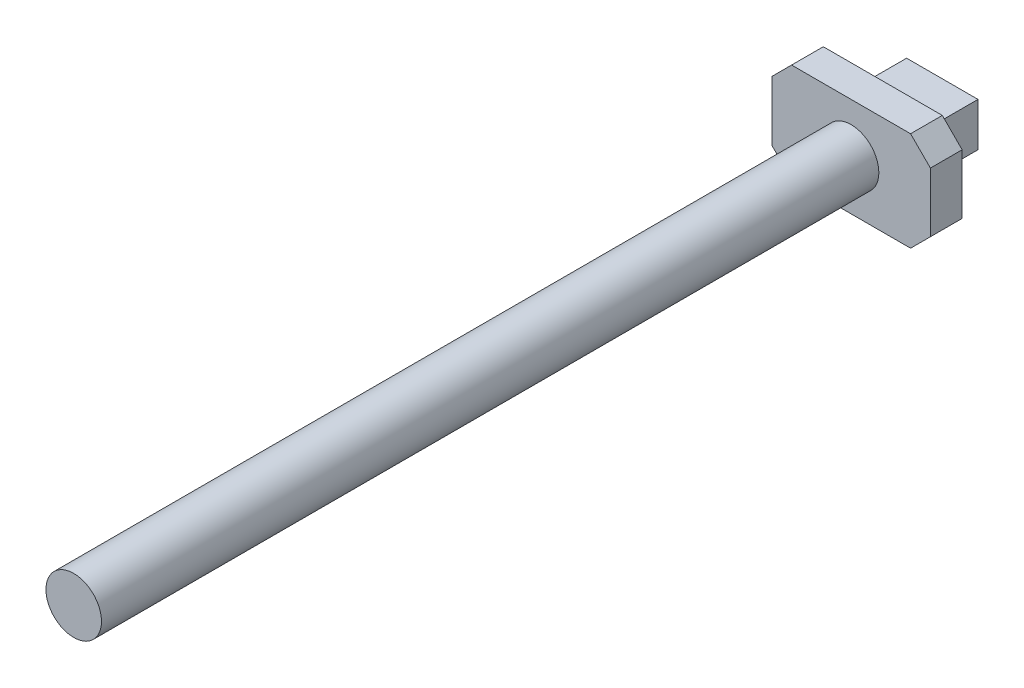
SolidWorks part; units mm, degrees
ref_plane "前视基准面" through (0, 0, 0) normal (0, 0, 1) x (1, 0, 0)
ref_plane "上视基准面" through (0, 0, 0) normal (0, 1, 0) x (1, 0, 0)
ref_plane "右视基准面" through (0, 0, 0) normal (1, 0, 0) x (0, 0, -1)
sketch "草图1" plane through (0, 0, 0) normal (0, 0, 1) x (1, 0, 0)
  circle A0 centre (0, 0) radius 7
extrude "凸台-拉伸1" add sketch "草图1" along normal blind 160 and the other way blind 36
sketch "草图2" plane through (0, 0, -36) normal (0, 0, -1) x (-1, 0, 0)
  line L0 (15, 12.5) -> (20, 7.5)
  line L1 (-20, 12.5) -> (20, 12.5)
  line L2 (-20, 12.5) -> (-20, -12.5)
  line L3 (-20, -12.5) -> (20, -12.5)
  line L4 (20, 12.5) -> (20, -12.5)
  line L5 (-20, 12.5) -> (20, -12.5) construction
  line L6 (-20, -12.5) -> (20, 12.5) construction
  line L7 (-15, 12.5) -> (-20, 7.5)
  line L8 (-20, -7.5) -> (-15, -12.5)
  line L9 (-15, -12.5) -> (15, -12.5)
  line L10 (15, -12.5) -> (20, -7.5)
  point P0 (0, 0)
  circle M1 centre (0, 0) radius 7
  dimension "D1" = 25
  dimension "D2" = 40
  dimension "D3" = 5
  dimension "D4" = 5
  dimension "D5" = 5
  dimension "D6" = 5
  dimension "D7" = 5
  dimension "D8" = 5
  dimension "D9" = 5
  dimension "D10" = 5
extrude "凸台-拉伸2" add sketch "草图2" along normal blind 8 contours L3 L10 L4 L0 L1 L7 L2 L8 M1 | M1
sketch "草图3" plane through (0, 0, -44) normal (0, 0, -1) x (-1, 0, 0)
  line L1 (9, 5.5) -> (-9, 5.5)
  line L2 (9, 5.5) -> (9, -5.5)
  line L3 (9, -5.5) -> (-9, -5.5)
  line L4 (-9, 5.5) -> (-9, -5.5)
  line L5 (9, 5.5) -> (-9, -5.5) construction
  line L6 (9, -5.5) -> (-9, 5.5) construction
  point P0 (0, 0)
  dimension "D1" = 18
  dimension "D2" = 11
extrude "凸台-拉伸3" add sketch "草图3" along normal blind 15
sketch "草图4" plane through (0, 0, -59) normal (0, 0, -1) x (-1, 0, 0)
  line L1 (15, 12.5) -> (-15, 12.5)
  line L2 (15, 12.5) -> (15, -12.5)
  line L3 (15, -12.5) -> (-15, -12.5)
  line L4 (-15, 12.5) -> (-15, -12.5)
  line L5 (15, 12.5) -> (-15, -12.5) construction
  line L6 (15, -12.5) -> (-15, 12.5) construction
  circle A0 centre (15, 0) radius 12.5
  circle A1 centre (-15, 0) radius 12.5
  point P0 (0, 0)
  line M1 (-9, 5.5) -> (-9, -5.5)
  line M2 (-9, -5.5) -> (9, -5.5)
  line M3 (9, -5.5) -> (9, 5.5)
  line M4 (9, 5.5) -> (-9, 5.5)
  dimension "D1" = 25
  dimension "D2" = 30
extrude "凸台-拉伸4" add sketch "草图4" along normal blind 30 contours L4 A1 | A1 L4 M4 M2 M1 | A1 M2 M4 M1 | A1 A0 M2 M4 | A0 M4 M2 M3 | L2 A0 M4 M3 M2 | L2 A0 | A1 L3 A0 M2 | A1 A0 L1 M4
sketch "草图5" plane through (0, 0, -89) normal (0, 0, -1) x (-1, 0, 0)
  line L1 (30, 20) -> (-30, 20)
  line L2 (30, 20) -> (30, -20)
  line L3 (30, -20) -> (-30, -20)
  line L4 (-30, 20) -> (-30, -20)
  line L5 (30, 20) -> (-30, -20) construction
  line L6 (30, -20) -> (-30, 20) construction
  point P0 (0, 0)
  dimension "D1" = 60
  dimension "D2" = 40
extrude "凸台-拉伸5" add sketch "草图5" along normal blind 6
sketch "草图6" plane through (0, 0, -95) normal (0, 0, -1) x (-1, 0, 0)
  line L0 (-30, 20) -> (-30, -20) construction
  line L1 (30, 20) -> (-30, 20)
  line L2 (30, 20) -> (30, 14)
  line L3 (30, 14) -> (-30, 14)
  line L4 (-30, 20) -> (-30, 14)
  line L5 (30, -20) -> (30, 20) construction
  line L6 (-30, -20) -> (30, -20)
  line L7 (-30, -20) -> (-30, -14)
  line L8 (-30, -14) -> (30, -14)
  line L9 (30, -20) -> (30, -14)
  dimension "D1" = 6
  dimension "D2" = 6
extrude "凸台-拉伸6" add sketch "草图6" along normal blind 60
sketch "草图7" plane through (-30, 0, 0) normal (-1, 0, 0) x (0, 0, 1)
  line L0 (-155, 14) -> (-95, 14) construction
  line L1 (-125, 14) -> (-160, 14)
  line L2 (-125, 14) -> (-125, 8)
  line L3 (-125, 8) -> (-160, 8)
  line L4 (-160, 14) -> (-160, 8)
  line L5 (-155, -14) -> (-95, -14) construction
  line L6 (-125, -14) -> (-160, -14)
  line L7 (-125, -14) -> (-125, -8)
  line L8 (-125, -8) -> (-160, -8)
  line L9 (-160, -14) -> (-160, -8)
  line L11 (-160, 14) -> (-166, 14)
  line L12 (-160, 14) -> (-160, -14)
  line L13 (-160, -14) -> (-166, -14)
  line L14 (-166, 14) -> (-166, -14)
  line L15 (-166, 0) -> (-195.4559, 0)
  line L16 (-166, 0) -> (-166, 4)
  line L17 (-166, 4) -> (-195.4559, 4)
  line L18 (-195.4559, 0) -> (-195.4559, 4)
  line L19 (-166, 0) -> (-195.4559, 0)
  line L20 (-166, 0) -> (-166, -4)
  line L21 (-166, -4) -> (-195.4559, -4)
  line L22 (-195.4559, 0) -> (-195.4559, -4)
  line M4 (-155, 14) -> (-95, 14)
  line M6 (-95, -14) -> (-155, -14)
  dimension "D1" = 6
  dimension "D2" = 6
  dimension "D3" = 6
  dimension "D4" = 35
  dimension "D5" = 4
  dimension "D6" = 4
extrude "凸台-拉伸7" add sketch "草图7" against normal blind 8 contours L1 L4 L3 L2 M4 | L9 L6 L7 L8 M6 | L11 L14 L13 L9 L12 L4 | L15 L22 L21 L14 | L18 L15 L14 L17
pattern_linear "阵列(线性)1" count 2 spacing 52 along (1, 0, 0) of "凸台-拉伸7"
sketch "草图8" plane through (0, 0, -59) normal (0, 0, 1) x (1, 0, 0)
  line L1 (-59.2019, 47.5924) -> (59.2019, 47.5924)
  line L2 (-59.2019, 47.5924) -> (-59.2019, -47.5924)
  line L3 (-59.2019, -47.5924) -> (59.2019, -47.5924)
  line L4 (59.2019, 47.5924) -> (59.2019, -47.5924)
  line L5 (-59.2019, 47.5924) -> (59.2019, -47.5924) construction
  line L6 (-59.2019, -47.5924) -> (59.2019, 47.5924) construction
  point P0 (0, 0)
extrude "切除-拉伸1" cut sketch "草图8" against normal blind 200
